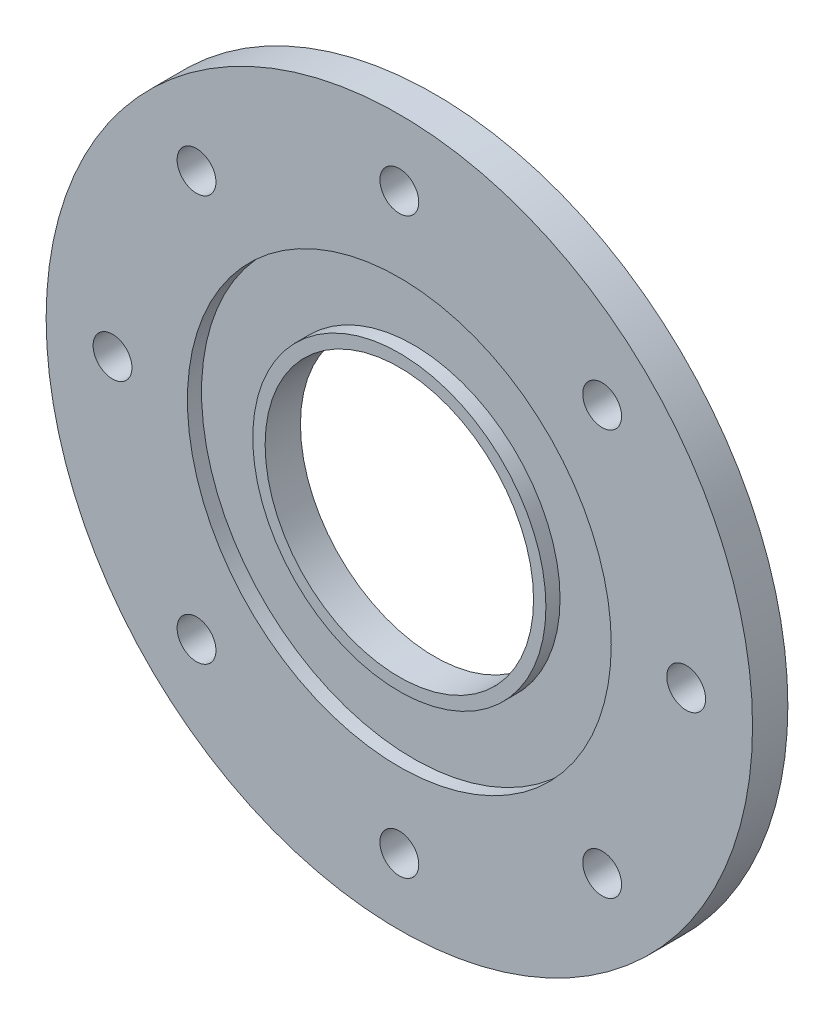
SolidWorks part; units mm, degrees
ref_plane "Alzado" through (0, 0, 0) normal (0, 0, 1) x (1, 0, 0)
ref_plane "Planta" through (0, 0, 0) normal (0, 1, 0) x (1, 0, 0)
ref_plane "Vista lateral" through (0, 0, 0) normal (1, 0, 0) x (0, 0, -1)
sketch "Croquis1" plane through (0, 0, 0) normal (0, 0, 1) x (1, 0, 0)
  circle A0 centre (0, 0) radius 50
  circle A1 centre (0, 0) radius 19
  dimension "D1" = 100
  dimension "D2" = 38
extrude "Saliente-Extruir1" add sketch "Croquis1" along normal blind 5
sketch "Croquis4" plane through (0, 0, 5) normal (0, 0, 1) x (1, 0, 0)
  circle A0 centre (0, 0) radius 20.75
  circle A1 centre (0, 0) radius 30
  dimension "D1" = 41.5
  dimension "D2" = 60
extrude "Cortar-Extruir1" cut sketch "Croquis4" against normal blind 2
sketch "Croquis5" plane through (0, 0, 5) normal (0, 0, 1) x (1, 0, 0)
  circle A0 centre (0, 0) radius 40.603
  circle A1 centre (40.603, 0) radius 2.75
  circle A2 centre (28.7107, -28.7107) radius 2.75
  circle A3 centre (0, -40.603) radius 2.75
  circle A4 centre (-28.7107, -28.7107) radius 2.75
  circle A5 centre (-40.603, 0) radius 2.75
  circle A6 centre (-28.7107, 28.7107) radius 2.75
  circle A7 centre (0, 40.603) radius 2.75
  circle A8 centre (28.7107, 28.7107) radius 2.75
  point P21 (0, 0)
  dimension "D2" = 5.5
  dimension "D1" = 8
extrude "Cortar-Extruir2" cut sketch "Croquis5" against normal up to surface (5 mm away) contours A1 | A8 | A7 | A6 | A5 | A4 | A3 | A2 up to face at (50, 0, 0)
